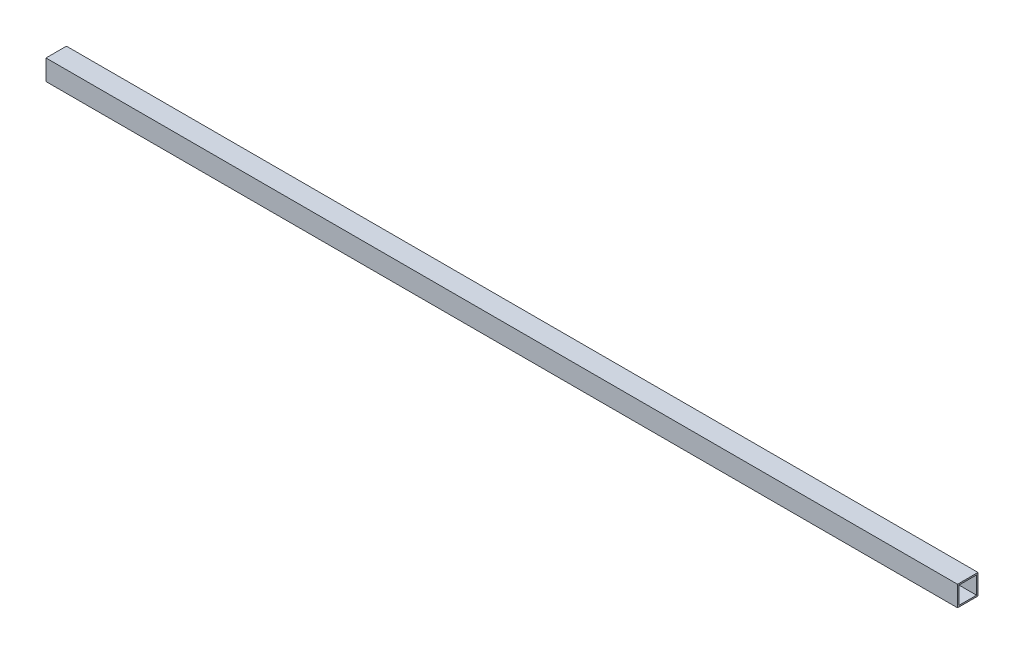
SolidWorks part; units mm, degrees
material "6061 Alloy"
ref_plane "Front Plane" through (0, 0, 0) normal (0, 0, 1) x (1, 0, 0)
ref_plane "Top Plane" through (0, 0, 0) normal (0, 1, 0) x (1, 0, 0)
ref_plane "Right Plane" through (0, 0, 0) normal (1, 0, 0) x (0, 0, -1)
sketch "Sketch1" plane through (0, 0, 0) normal (1, 0, 0) x (0, 0, -1)
  line L0 (41.275, 41.275) -> (3.175, 41.275)
  line L1 (0, 0) -> (44.45, 0)
  line L2 (44.45, 0) -> (44.45, 44.45)
  line L3 (44.45, 44.45) -> (0, 44.45)
  line L4 (0, 44.45) -> (0, 0)
  line L5 (3.175, 41.275) -> (3.175, 3.175)
  line L6 (3.175, 3.175) -> (41.275, 3.175)
  line L7 (41.275, 3.175) -> (41.275, 41.275)
  circle A0 centre (22.225, 22.225) radius 22.225 construction
  dimension "D1" = 44.45
  dimension "D2" = 3.175
extrude "Boss-Extrude1" add sketch "Sketch1" along normal mid plane 1981.2
equation "\"285n\"=28.25"
